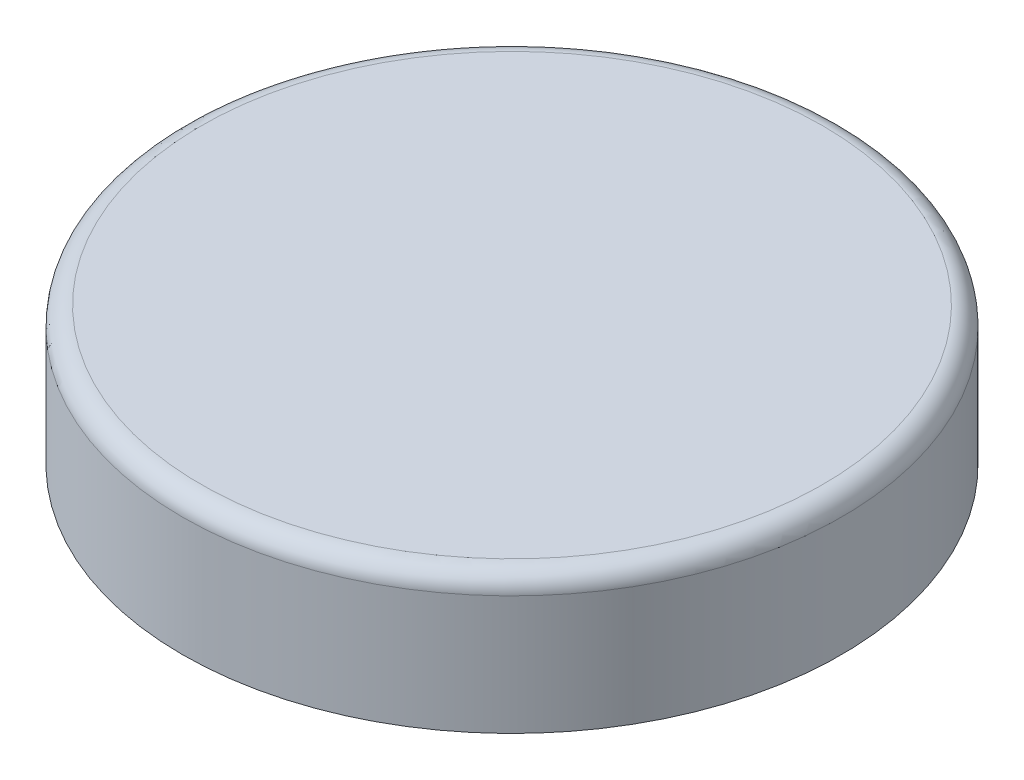
SolidWorks part; units mm, degrees
material "PVC Rigid"
ref_plane "Front" through (0, 0, 0) normal (0, 0, 1) x (1, 0, 0)
ref_plane "Top" through (0, 0, 0) normal (0, 1, 0) x (1, 0, 0)
ref_plane "Right" through (0, 0, 0) normal (1, 0, 0) x (0, 0, -1)
sketch "Sketch1" plane through (0, 0, 0) normal (1, 0, 0) x (0, 0, -1)
  line L0 (-161.925, 0) -> (161.925, 0) construction
  line L1 (-161.925, 0) -> (-162.1234, 0) construction
  line L2 (-162.1234, 0) -> (-166.8859, 0) construction
  line L3 (161.925, 0) -> (162.1234, 0) construction
  line L4 (162.1234, 0) -> (166.8859, 0) construction
  line L5 (0, 0) -> (0, 69.85)
  line L6 (-166.8859, 0) -> (-166.8859, 69.85)
  line L7 (-166.8859, 69.85) -> (166.8859, 69.85) construction
  line L8 (166.8859, 69.85) -> (166.8859, 0) construction
  line L9 (-166.8859, 69.85) -> (0, 69.85)
  line L10 (0, 0) -> (-166.8859, 0)
  dimension "D2" = 0.1984
revolve "Revolve1" add sketch "Sketch1" angle 360 about L5
fillet "Fillet1" radius 9.525 1 edges at (0, 69.85, -166.8859)
shell "Shell1" thickness 4.7625
equation "\"D1@Shell1\" = \"Wall Thickness@Sketch1\""
